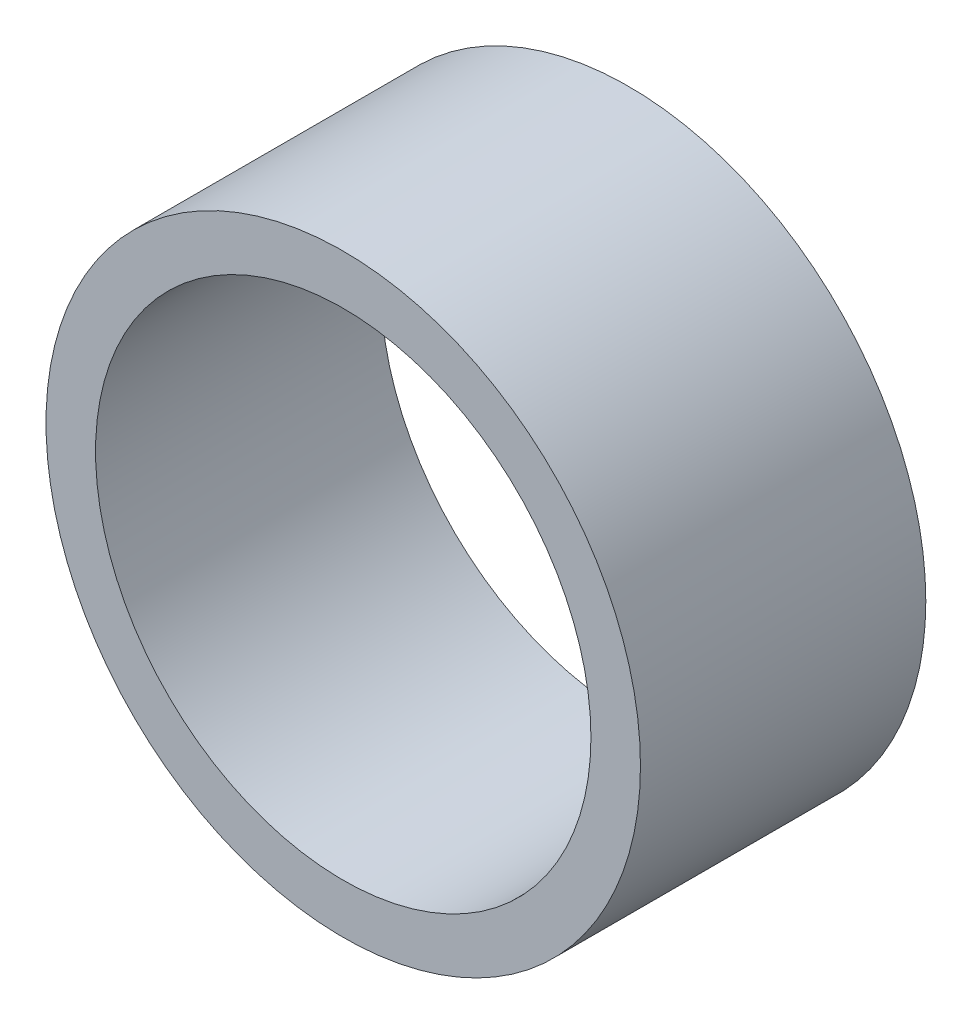
SolidWorks part; units mm, degrees
material "6061-T6 (SS)"
ref_plane "Płaszczyzna XY" through (0, 0, 0) normal (0, 0, 1) x (1, 0, 0)
ref_plane "Płaszczyzna XZ" through (0, 0, 0) normal (0, 1, 0) x (1, 0, 0)
ref_plane "Płaszczyzna YZ" through (0, 0, 0) normal (1, 0, 0) x (0, 0, -1)
sketch "Szkic1" plane through (0, 0, 0) normal (0, 0, 1) x (1, 0, 0)
  circle A0 centre (0, 0) radius 12.5
  circle A1 centre (0, 0) radius 15
  dimension "D1" = 25
  dimension "D2" = 30
extrude "Dodanie-wyciągnięcie1" add sketch "Szkic1" along normal blind 14.4
